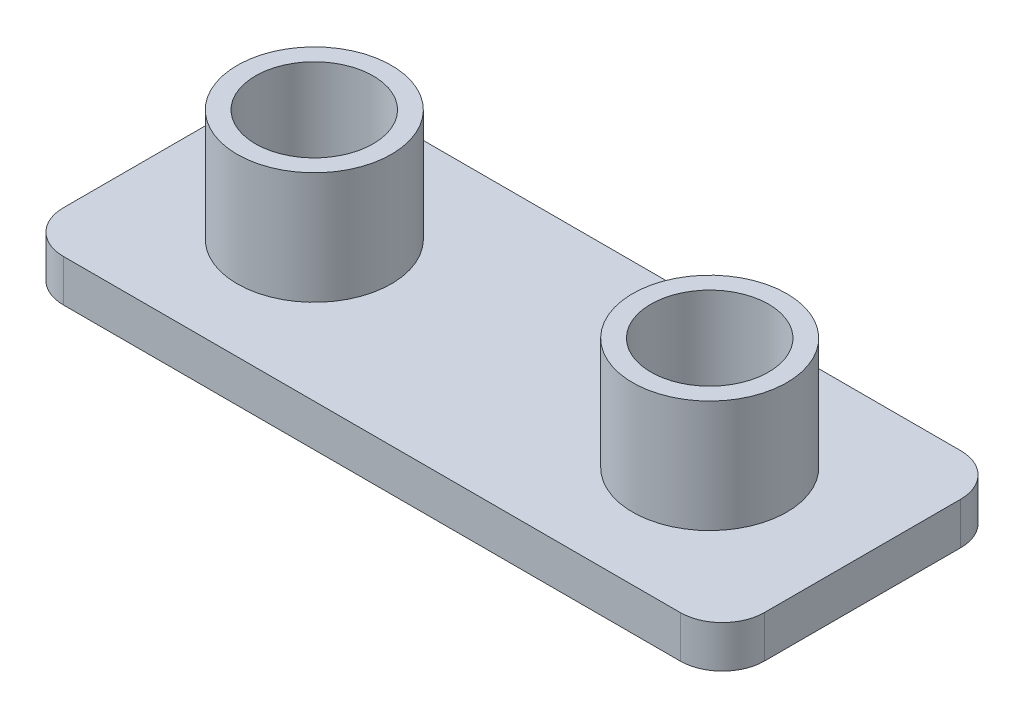
SolidWorks part; units mm, degrees
ref_plane "Front Plane" through (0, 0, 0) normal (0, 0, 1) x (1, 0, 0)
ref_plane "Top Plane" through (0, 0, 0) normal (0, 1, 0) x (1, 0, 0)
ref_plane "Right Plane" through (0, 0, 0) normal (1, 0, 0) x (0, 0, -1)
sketch "Sketch1" plane through (0, 0, 0) normal (0, 1, 0) x (1, 0, 0)
  line L1 (-11, 5) -> (11, 5)
  line L2 (-12.5, 3.5) -> (-12.5, -3.5)
  line L3 (-11, -5) -> (11, -5)
  line L4 (12.5, 3.5) -> (12.5, -3.5)
  line L5 (0, -5) -> (0, 5) construction
  line L6 (-12.5, 0) -> (12.5, 0) construction
  arc A0 (-12.5, -3.5) -> (-11, -5) centre (-11, -3.5) ccw
  arc A1 (11, -5) -> (12.5, -3.5) centre (11, -3.5) ccw
  arc A2 (11, 5) -> (12.5, 3.5) centre (11, 3.5) cw
  arc A3 (-11, 5) -> (-12.5, 3.5) centre (-11, 3.5) ccw
  circle A4 centre (-7.05, 0) radius 2.1
  circle A5 centre (7.05, 0) radius 2.1
  point P0 (0, 0)
  point P6 (-12.5, -5)
  point P11 (12.5, 5)
  point P15 (-12.5, 5)
  dimension "D3" = 1.5
  dimension "D5" = 4.2
  dimension "D1" = 10
  dimension "D2" = 25
  dimension "D4" = 7.05
extrude "Boss-Extrude1" add sketch "Sketch1" along normal blind 1.5
sketch "Sketch3" plane through (0, 1.5, 0) normal (0, 1, 0) x (1, 0, 0)
  line L0 (0, 5) -> (0, 0) construction
  line L1 (11, 5) -> (-11, 5) construction
  circle A0 centre (-7.05, 0) radius 2.1
  circle A1 centre (-7.05, 0) radius 2.75
  circle A2 centre (7.05, 0) radius 2.75
  circle A3 centre (7.05, 0) radius 2.1
  dimension "D1" = 5.5
  dimension "D2" = 4.2
extrude "Boss-Extrude2" add sketch "Sketch3" along normal blind 4
